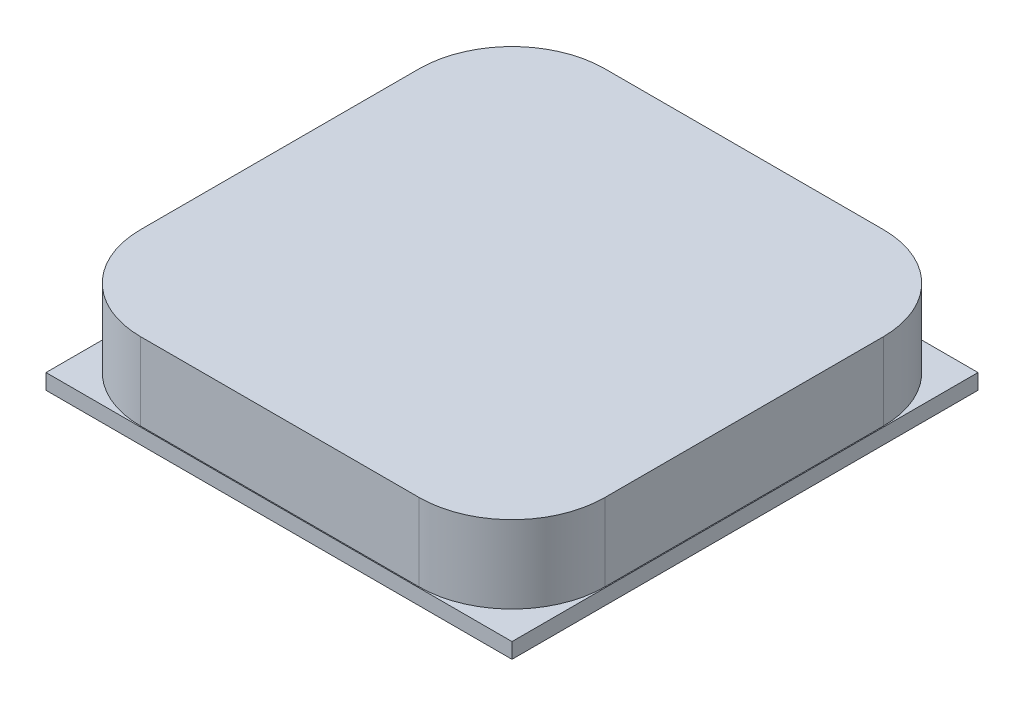
SolidWorks part; units mm, degrees
ref_plane "Front Plane" through (0, 0, 0) normal (0, 0, 1) x (1, 0, 0)
ref_plane "Top Plane" through (0, 0, 0) normal (0, 1, 0) x (1, 0, 0)
ref_plane "Right Plane" through (0, 0, 0) normal (1, 0, 0) x (0, 0, -1)
sketch "Sketch1" plane through (0, 0, 0) normal (0, 1, 0) x (1, 0, 0)
  line L1 (-12.55, -12.55) -> (12.55, -12.55)
  line L2 (-12.55, -12.55) -> (-12.55, 12.55)
  line L3 (-12.55, 12.55) -> (12.55, 12.55)
  line L4 (12.55, -12.55) -> (12.55, 12.55)
  line L5 (0, 12.55) -> (0, -12.55) construction
  line L6 (-12.55, 0) -> (12.55, 0) construction
  point P0 (0, 0)
  dimension "D1" = 25.1
extrude "Boss-Extrude1" add sketch "Sketch1" along normal blind 0.83
sketch "Sketch2" plane through (0, 0, 0) normal (0, 1, 0) x (1, 0, 0)
  line L1 (-12.5, -12.5) -> (12.5, -12.5)
  line L2 (-12.5, -12.5) -> (-12.5, 12.5)
  line L3 (-12.5, 12.5) -> (12.5, 12.5)
  line L4 (12.5, -12.5) -> (12.5, 12.5)
  line L5 (0, 12.5) -> (0, -12.5) construction
  line L6 (-12.5, 0) -> (12.5, 0) construction
  point P0 (0, 0)
  dimension "D1" = 25
extrude "Boss-Extrude2" add sketch "Sketch2" along normal blind 5
fillet "Fillet1" radius 5 4 edges at (-12.5, 2.915, 12.5) (-12.5, 2.915, -12.5) (12.5, 2.915, -12.5) (12.5, 2.915, 12.5)
sketch "Sketch3" plane through (0, 0, 0) normal (0, 1, 0) x (1, 0, 0)
  line L1 (-8, 7) -> (8, 7)
  line L2 (-8, 7) -> (-8, -7)
  line L3 (-8, -7) -> (8, -7)
  line L4 (8, 7) -> (8, -7)
  line L5 (0, -7) -> (0, 7) construction
  line L6 (-8, 0) -> (8, 0) construction
  line L7 (8, 1.5) -> (5, 1.5)
  line L8 (8, 1.5) -> (8, -1.5)
  line L9 (8, -1.5) -> (5, -1.5)
  line L10 (5, 1.5) -> (5, -1.5)
  point P0 (0, 0)
  point P8 (5, 0)
  dimension "D1" = 16
  dimension "D2" = 14
  dimension "D3" = 3
extrude "Boss-Extrude3" add sketch "Sketch3" against normal blind 2.4 contours L10 L7 L4 L1 L2 L3 L9
chamfer "Chamfer1" distance 0.5 angle 45 2 edges at (0, 0, -7) (0, 0, 7)
